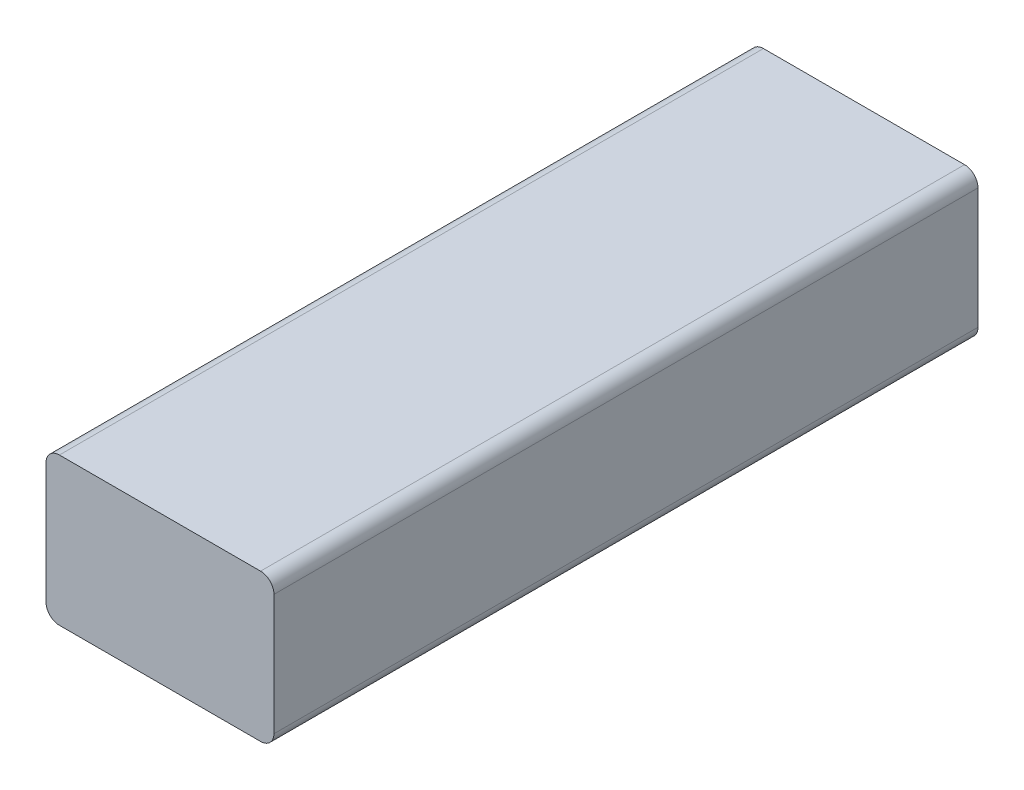
SolidWorks part; units mm, degrees
ref_plane "Front Plane" through (0, 0, 0) normal (0, 0, 1) x (1, 0, 0)
ref_plane "Top Plane" through (0, 0, 0) normal (0, 1, 0) x (1, 0, 0)
ref_plane "Right Plane" through (0, 0, 0) normal (1, 0, 0) x (0, 0, -1)
sketch "Sketch1" plane through (0, 0, 0) normal (0, 0, 1) x (1, 0, 0)
  line L1 (2, 0) -> (32, 0)
  line L2 (0, 2) -> (0, 20)
  line L3 (2, 22) -> (32, 22)
  line L4 (34, 2) -> (34, 20)
  arc A0 (0, 20) -> (2, 22) centre (2, 20) cw
  arc A1 (2, 0) -> (0, 2) centre (2, 2) cw
  arc A2 (34, 2) -> (32, 0) centre (32, 2) cw
  arc A3 (34, 20) -> (32, 22) centre (32, 20) ccw
  point P9 (0, 0)
  dimension "D1" = 2
  dimension "D2" = 2
  dimension "D3" = 2
  dimension "D4" = 2
extrude "Boss-Extrude1" add sketch "Sketch1" along normal blind 105
sketch "Sketch2" plane through (0, 22, 0) normal (0, 1, 0) x (1, 0, 0)
  circle A0 centre (17, -52.5) radius 6.2972
